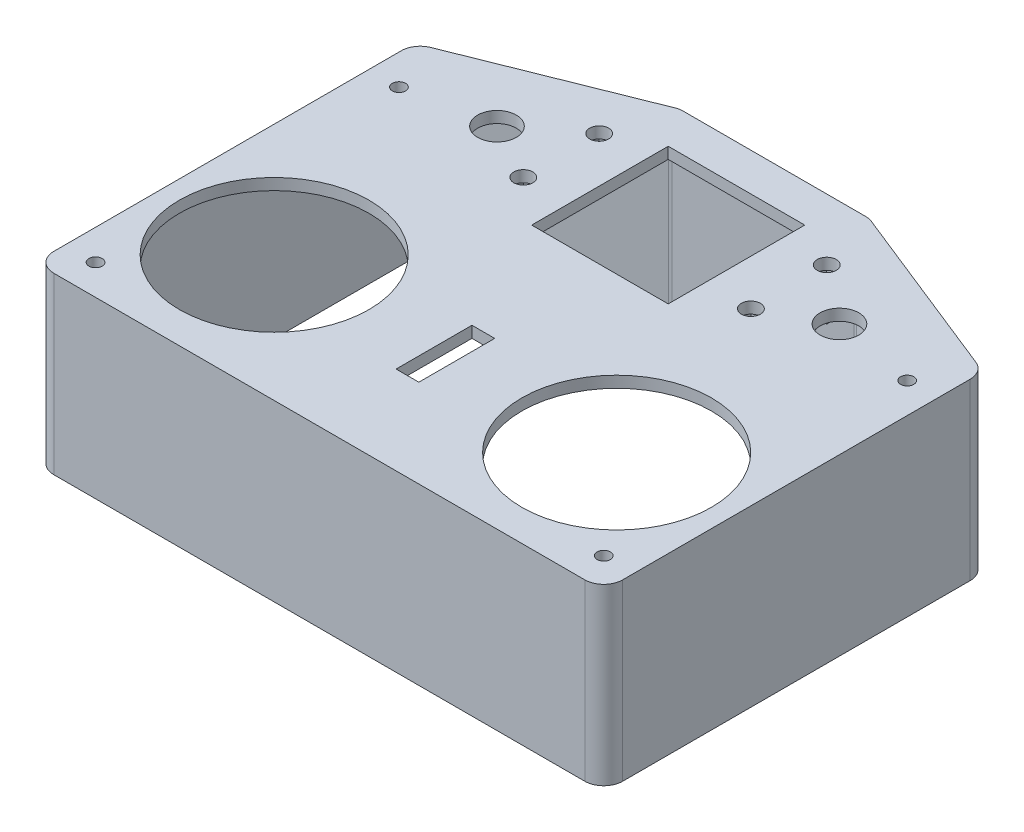
SolidWorks part; units mm, degrees
ref_plane "Front Plane" through (0, 0, 0) normal (0, 0, 1) x (1, 0, 0)
ref_plane "Top Plane" through (0, 0, 0) normal (0, 1, 0) x (1, 0, 0)
ref_plane "Right Plane" through (0, 0, 0) normal (1, 0, 0) x (0, 0, -1)
sketch "Sketch1" plane through (0, 0, 0) normal (0, 1, 0) x (1, 0, 0)
  line L0 (-5.8336, 22.0213) -> (13.8664, 22.0213) construction
  line L1 (13.8664, 22.0213) -> (13.8664, -4.4787) construction
  line L2 (13.8664, -4.4787) -> (-5.8336, -4.4787) construction
  line L3 (-5.8336, -4.4787) -> (-5.8336, 22.0213) construction
  line L4 (4.0164, 22.0213) -> (4.0164, -4.4787) construction
  line L5 (-5.8336, 8.7713) -> (13.8664, 8.7713) construction
  line L6 (49.1664, 75.5213) -> (49.1664, -24.4787) construction
  line L7 (-20.8336, -24.4787) -> (119.1664, -24.4787)
  line L8 (-25.8336, -19.4787) -> (-25.8336, 72.1361)
  line L10 (124.1664, -19.4787) -> (124.1664, 72.1361)
  line L11 (25.1293, 95.5213) -> (73.2035, 95.5213)
  line L12 (-22.6906, 76.7785) -> (23.2723, 95.1636)
  line L13 (121.0233, 76.7785) -> (75.0604, 95.1636)
  line L14 (-25.8336, 67.5213) -> (124.1664, 67.5213) construction
  line L15 (31.1664, 85.5213) -> (67.1664, 85.5213)
  line L16 (31.1664, 85.5213) -> (31.1664, 49.5213)
  line L17 (31.1664, 49.5213) -> (67.1664, 49.5213)
  line L18 (67.1664, 85.5213) -> (67.1664, 49.5213)
  line L19 (4.0164, 67.5213) -> (4.0164, 90.5213) construction
  line L21 (46.1664, -1.2287) -> (52.1664, -1.2287)
  line L22 (46.1664, -1.2287) -> (46.1664, 18.7713)
  line L23 (46.1664, 18.7713) -> (52.1664, 18.7713)
  line L24 (52.1664, -1.2287) -> (52.1664, 18.7713)
  line L25 (46.1664, -1.2287) -> (52.1664, 18.7713) construction
  line L26 (46.1664, 18.7713) -> (52.1664, -1.2287) construction
  circle A0 centre (-5.8336, 22.0213) radius 1.65 construction
  circle A1 centre (13.8664, 22.0213) radius 1.65 construction
  circle A2 centre (-5.8336, -4.4787) radius 1.65 construction
  circle A3 centre (13.8664, -4.4787) radius 1.65 construction
  circle A4 centre (4.0164, 8.7713) radius 25
  circle A5 centre (84.4664, -4.4787) radius 1.65 construction
  circle A6 centre (104.1664, -4.4787) radius 1.65 construction
  circle A7 centre (104.1664, 22.0213) radius 1.65 construction
  circle A8 centre (84.4664, 22.0213) radius 1.65 construction
  circle A9 centre (94.3164, 8.7713) radius 25
  arc A10 (-20.8336, -24.4787) -> (-25.8336, -19.4787) centre (-20.8336, -19.4787) cw
  arc A11 (124.1664, -19.4787) -> (119.1664, -24.4787) centre (119.1664, -19.4787) cw
  arc A12 (124.1664, 72.1361) -> (121.0233, 76.7785) centre (119.1664, 72.1361) ccw
  arc A13 (75.0604, 95.1636) -> (73.2035, 95.5213) centre (73.2035, 90.5213) ccw
  arc A14 (25.1293, 95.5213) -> (23.2723, 95.1636) centre (25.1293, 90.5213) ccw
  arc A15 (-22.6906, 76.7785) -> (-25.8336, 72.1361) centre (-20.8336, 72.1361) ccw
  circle A16 centre (4.0164, 67.5213) radius 5.1
  circle A17 centre (94.3164, 67.5213) radius 5.1
  circle A18 centre (19.1664, 79.3161) radius 2.5
  circle A19 centre (19.1664, 59.3161) radius 2.5
  circle A20 centre (79.1664, 59.3161) radius 2.5
  circle A21 centre (79.1664, 79.3161) radius 2.5
  point P34 (-25.8336, -24.4787)
  point P37 (124.1664, -24.4787)
  point P42 (74.1664, 95.5213)
  point P45 (24.1664, 95.5213)
  point P48 (-25.8336, 75.5213)
  point P68 (49.1664, 8.7713)
  dimension "D1" = 3.3
  dimension "D2" = 19.7
  dimension "D5" = 50
  dimension "D16" = 5
  dimension "D21" = 10.2
  dimension "D22" = 5
  dimension "D23" = 5
  dimension "D25" = 12
  dimension "D3" = 26.5
  dimension "D4" = 19.7
  dimension "D6" = 20
  dimension "D7" = 150
  dimension "D8" = 100
  dimension "D9" = 20
  dimension "D10" = 29.85
  dimension "D11" = 50
  dimension "D12" = 25
  dimension "D13" = 29.85
  dimension "D14" = 33.25
  dimension "D15" = 33.25
  dimension "D17" = 36
  dimension "D18" = 36
  dimension "D19" = 18
  dimension "D20" = 10
  dimension "D24" = 12
  dimension "D26" = 20
  dimension "D27" = 20
  dimension "D28" = 10
  dimension "D29" = 6
  dimension "D30" = 3
extrude "Boss-Extrude1" add sketch "Sketch1" along normal blind 3
sketch "Sketch2" plane through (0, 0, 0) normal (0, -1, 0) x (1, 0, 0)
  line L0 (119.1664, 21.4787) -> (-20.8336, 21.4787)
  line L1 (-22.8336, 19.4787) -> (-22.8336, -72.1361)
  line L2 (-21.5764, -73.993) -> (24.3865, -92.3782)
  line L3 (25.1293, -92.5213) -> (73.2035, -92.5213)
  line L4 (73.9462, -92.3782) -> (119.9092, -73.993)
  line L5 (121.1664, -72.1361) -> (121.1664, 19.4787)
  line L6 (-25.8336, 19.4787) -> (-25.8336, -72.1361)
  line L7 (-22.6906, -76.7785) -> (23.2723, -95.1636)
  line L8 (25.1293, -95.5213) -> (73.2035, -95.5213)
  line L9 (75.0604, -95.1636) -> (121.0233, -76.7785)
  line L10 (124.1664, -72.1361) -> (124.1664, 19.4787)
  line L11 (119.1664, 24.4787) -> (-20.8336, 24.4787)
  line L12 (-25.8336, 19.4787) -> (-25.8336, -72.1361)
  line L13 (-22.6906, -76.7785) -> (23.2723, -95.1636)
  line L14 (25.1293, -95.5213) -> (73.2035, -95.5213)
  line L15 (75.0604, -95.1636) -> (121.0233, -76.7785)
  line L16 (124.1664, -72.1361) -> (124.1664, 19.4787)
  line L17 (119.1664, 24.4787) -> (-20.8336, 24.4787)
  arc A0 (-20.8336, 21.4787) -> (-22.8336, 19.4787) centre (-20.8336, 19.4787) ccw
  arc A1 (-22.8336, -72.1361) -> (-21.5764, -73.993) centre (-20.8336, -72.1361) ccw
  arc A2 (24.3865, -92.3782) -> (25.1293, -92.5213) centre (25.1293, -90.5213) ccw
  arc A3 (73.2035, -92.5213) -> (73.9462, -92.3782) centre (73.2035, -90.5213) ccw
  arc A4 (119.9092, -73.993) -> (121.1664, -72.1361) centre (119.1664, -72.1361) ccw
  arc A5 (121.1664, 19.4787) -> (119.1664, 21.4787) centre (119.1664, 19.4787) ccw
  arc A6 (-20.8336, 24.4787) -> (-25.8336, 19.4787) centre (-20.8336, 19.4787) ccw
  arc A7 (-25.8336, -72.1361) -> (-22.6906, -76.7785) centre (-20.8336, -72.1361) ccw
  arc A8 (23.2723, -95.1636) -> (25.1293, -95.5213) centre (25.1293, -90.5213) ccw
  arc A9 (73.2035, -95.5213) -> (75.0604, -95.1636) centre (73.2035, -90.5213) ccw
  arc A10 (121.0233, -76.7785) -> (124.1664, -72.1361) centre (119.1664, -72.1361) ccw
  arc A11 (124.1664, 19.4787) -> (119.1664, 24.4787) centre (119.1664, 19.4787) ccw
  arc A12 (-20.8336, 24.4787) -> (-25.8336, 19.4787) centre (-20.8336, 19.4787) ccw
  arc A13 (-25.8336, -72.1361) -> (-22.6906, -76.7785) centre (-20.8336, -72.1361) ccw
  arc A14 (23.2723, -95.1636) -> (25.1293, -95.5213) centre (25.1293, -90.5213) ccw
  arc A15 (73.2035, -95.5213) -> (75.0604, -95.1636) centre (73.2035, -90.5213) ccw
  arc A16 (121.0233, -76.7785) -> (124.1664, -72.1361) centre (119.1664, -72.1361) ccw
  arc A17 (124.1664, 19.4787) -> (119.1664, 24.4787) centre (119.1664, 19.4787) ccw
  dimension "D1" = 0
  dimension "D2" = 3
extrude "Boss-Extrude2" add sketch "Sketch2" along normal blind 43
sketch "Sketch4" plane through (0, 0, 0) normal (0, -1, 0) x (1, 0, 0)
  line L0 (84.6664, -73.8161) -> (84.6664, -84.8161)
  line L1 (75.6664, -75.8161) -> (82.6664, -75.8161)
  line L2 (75.6664, -75.8161) -> (75.6664, -82.8161)
  line L3 (75.6664, -82.8161) -> (82.6664, -82.8161)
  line L4 (82.6664, -75.8161) -> (82.6664, -82.8161)
  line L5 (75.6664, -75.8161) -> (82.6664, -82.8161) construction
  line L6 (75.6664, -82.8161) -> (82.6664, -75.8161) construction
  line L7 (73.6664, -84.8161) -> (84.6664, -84.8161)
  line L8 (73.6664, -73.8161) -> (73.6664, -84.8161)
  line L9 (73.6664, -73.8161) -> (84.6664, -73.8161)
  line L10 (73.6664, -64.8161) -> (84.6664, -64.8161)
  line L11 (75.6664, -55.8161) -> (82.6664, -55.8161)
  line L12 (75.6664, -55.8161) -> (75.6664, -62.8161)
  line L13 (75.6664, -62.8161) -> (82.6664, -62.8161)
  line L14 (82.6664, -55.8161) -> (82.6664, -62.8161)
  line L15 (75.6664, -55.8161) -> (82.6664, -62.8161) construction
  line L16 (75.6664, -62.8161) -> (82.6664, -55.8161) construction
  line L17 (84.6664, -53.8161) -> (84.6664, -64.8161)
  line L18 (73.6664, -53.8161) -> (84.6664, -53.8161)
  line L19 (73.6664, -53.8161) -> (73.6664, -64.8161)
  line L20 (13.6664, -64.8161) -> (24.6664, -64.8161)
  line L21 (15.6664, -75.8161) -> (22.6664, -75.8161)
  line L22 (15.6664, -75.8161) -> (15.6664, -82.8161)
  line L23 (15.6664, -82.8161) -> (22.6664, -82.8161)
  line L24 (22.6664, -75.8161) -> (22.6664, -82.8161)
  line L25 (15.6664, -75.8161) -> (22.6664, -82.8161) construction
  line L26 (15.6664, -82.8161) -> (22.6664, -75.8161) construction
  line L27 (15.6664, -55.8161) -> (22.6664, -55.8161)
  line L28 (15.6664, -55.8161) -> (15.6664, -62.8161)
  line L29 (15.6664, -62.8161) -> (22.6664, -62.8161)
  line L30 (22.6664, -55.8161) -> (22.6664, -62.8161)
  line L31 (15.6664, -55.8161) -> (22.6664, -62.8161) construction
  line L32 (15.6664, -62.8161) -> (22.6664, -55.8161) construction
  line L33 (24.6664, -53.8161) -> (24.6664, -64.8161)
  line L34 (13.6664, -53.8161) -> (24.6664, -53.8161)
  line L35 (13.6664, -53.8161) -> (13.6664, -64.8161)
  line L36 (13.6664, -73.8161) -> (24.6664, -73.8161)
  line L37 (24.6664, -73.8161) -> (24.6664, -84.8161)
  line L38 (13.6664, -84.8161) -> (24.6664, -84.8161)
  line L39 (13.6664, -73.8161) -> (13.6664, -84.8161)
  point P0 (79.1664, -79.3161)
  point P10 (79.1664, -59.3161)
  point P20 (19.1664, -79.3161)
  point P26 (19.1664, -59.3161)
  dimension "D1" = 7
  dimension "D2" = 7
  dimension "D3" = 2
  dimension "D4" = 7
  dimension "D5" = 7
  dimension "D7" = 7
  dimension "D8" = 7
  dimension "D9" = 7
  dimension "D10" = 7
  dimension "D6" = 2
  dimension "D11" = 2
extrude "Boss-Extrude3" add sketch "Sketch4" along normal blind 5
sketch "Sketch5" plane through (0, 0, 0) normal (0, -1, 0) x (1, 0, 0)
  line L0 (119.1664, 21.4787) -> (-20.8336, 21.4787) construction
  line L1 (-22.8336, 19.4787) -> (-22.8336, -72.1361) construction
  line L2 (121.1664, -72.1361) -> (121.1664, 19.4787) construction
  circle A0 centre (-17.8336, 16.4787) radius 1.75
  circle A1 centre (116.1664, 16.4787) radius 1.75
  circle A2 centre (-17.8336, -63.5213) radius 1.75
  circle A3 centre (116.1664, -63.5213) radius 1.75
  dimension "D1" = 3.5
  dimension "D4" = 3.5
  dimension "D7" = 3.5
  dimension "D10" = 3.5
  dimension "D2" = 5
  dimension "D3" = 5
  dimension "D5" = 5
  dimension "D6" = 5
  dimension "D8" = 5
  dimension "D9" = 80
  dimension "D11" = 80
extrude "Cut-Extrude1" cut sketch "Sketch5" against normal blind 5
sketch "Sketch6" plane through (0, 0, -95.5213) normal (0, 0, -1) x (-1, 0, 0)
  line L0 (-49.1664, 3) -> (-49.1664, -43) construction
  line L1 (-73.2035, 3) -> (-25.1293, 3) construction
  line L2 (-25.1293, -43) -> (-73.2035, -43) construction
  circle A0 centre (-49.1664, -29.5) radius 3.5
  dimension "D1" = 7
  dimension "D2" = 13.5
extrude "Cut-Extrude2" cut sketch "Sketch6" against normal up to surface (3 mm away) up to face at (49.1664, -21.5, -92.5213)
